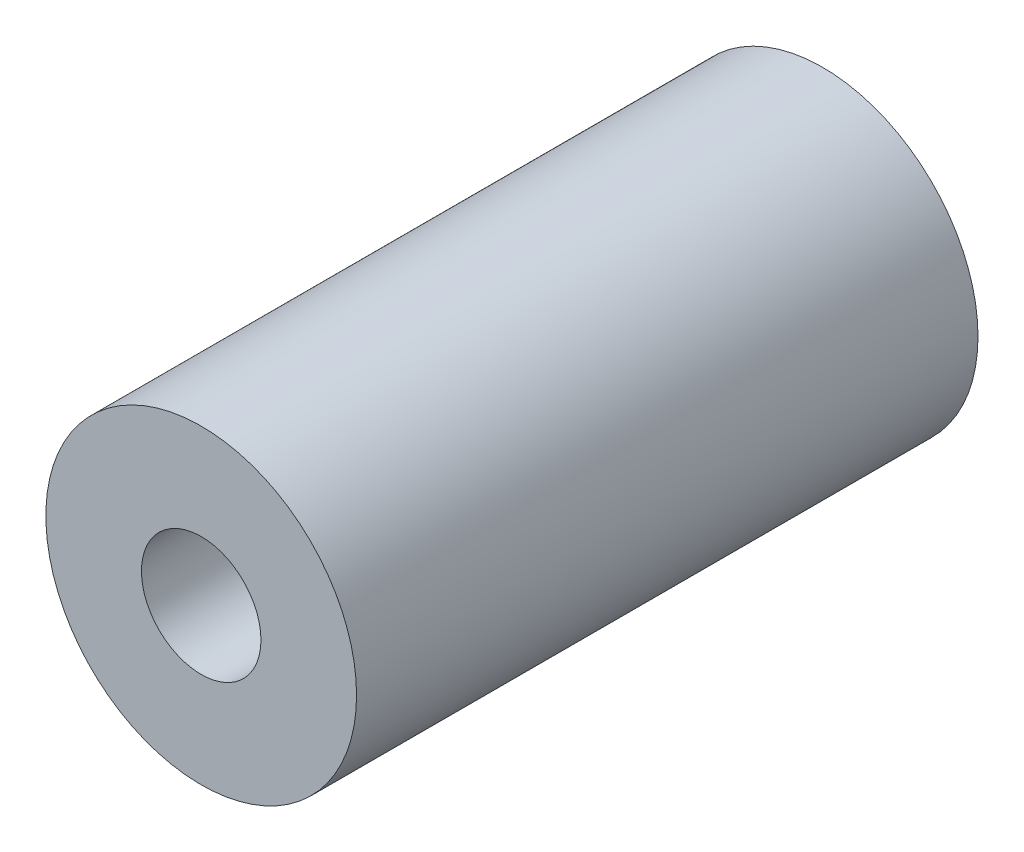
SolidWorks part; units mm, degrees
ref_plane "前视基准面" through (0, 0, 0) normal (0, 0, 1) x (1, 0, 0)
ref_plane "上视基准面" through (0, 0, 0) normal (0, 1, 0) x (1, 0, 0)
ref_plane "右视基准面" through (0, 0, 0) normal (1, 0, 0) x (0, 0, -1)
other "Configuration Table"
sketch "草图1" plane through (0, 0, 0) normal (0, 0, 1) x (1, 0, 0)
  circle A0 centre (0, 0) radius 1.25
  circle A1 centre (0, 0) radius 3.25
  dimension "D1" = 2.5
  dimension "D2" = 2
extrude "凸台-拉伸1" add sketch "草图1" along normal blind 13
